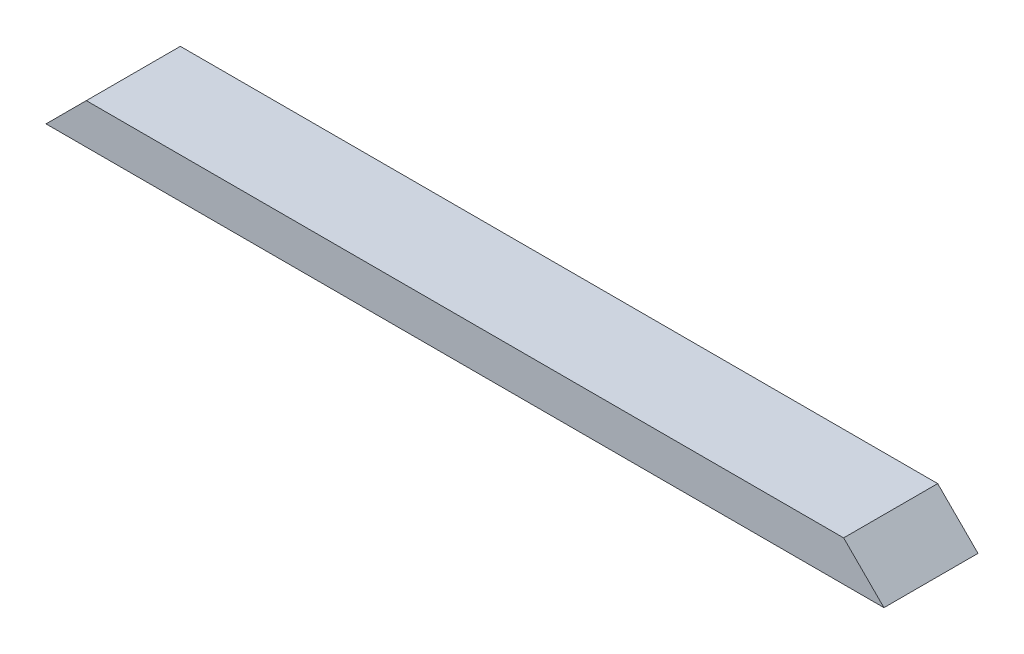
SolidWorks part; units mm, degrees
material "Pine"
ref_plane "Front Plane" through (0, 0, 0) normal (0, 0, 1) x (1, 0, 0)
ref_plane "Top Plane" through (0, 0, 0) normal (0, 1, 0) x (1, 0, 0)
ref_plane "Right Plane" through (0, 0, 0) normal (1, 0, 0) x (0, 0, -1)
sketch "Sketch1" plane through (0, 0, 0) normal (0, 1, 0) x (1, 0, 0)
  line L1 (0, 0) -> (792.1752, 0)
  line L2 (0, 0) -> (0, 88.9)
  line L3 (0, 88.9) -> (792.1752, 88.9)
  line L4 (792.1752, 0) -> (792.1752, 88.9)
  dimension "D1" = 88.9
  dimension "D2" = 792.1752
extrude "Boss-Extrude1" add sketch "Sketch1" along normal blind 38.1
sketch "Sketch2" plane through (0, 0, 0) normal (0, 0, 1) x (1, 0, 0)
  line L0 (0, 0) -> (38.1, 38.1)
  line L1 (0, 38.1) -> (792.1752, 38.1) construction
  line L2 (38.1, 38.1) -> (0, 38.1)
  line L3 (0, 38.1) -> (0, 0)
  line L5 (792.1752, 0) -> (792.1752, 38.1)
  line L9 (792.1752, 38.1) -> (754.0752, 38.1)
  line L10 (754.0752, 38.1) -> (792.1752, 0)
  dimension "D1" = 38.1
  dimension "D2" = 38.1
  dimension "D3" = 38.1
extrude "Cut-Extrude1" cut sketch "Sketch2" against normal through all
